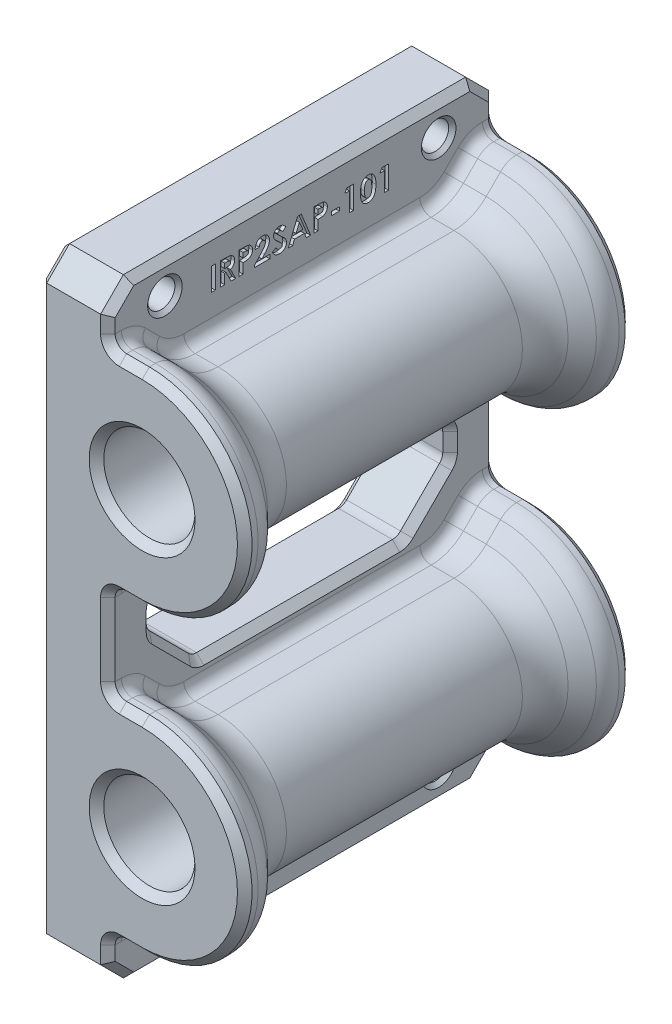
SolidWorks part; units mm, degrees
material "6061-T6 (SS)"
ref_plane "Front" through (0, 0, 0) normal (0, 0, 1) x (1, 0, 0)
ref_plane "Top" through (0, 0, 0) normal (0, 1, 0) x (1, 0, 0)
ref_plane "Right" through (0, 0, 0) normal (1, 0, 0) x (0, 0, -1)
sketch "Sketch1" plane through (0, 0, 0) normal (0, 0, 1) x (1, 0, 0)
  line L0 (0, 0) -> (0, -84.7725)
  line L1 (0, -84.7725) -> (14.2875, -84.7725)
  line L2 (14.2875, -84.7725) -> (14.2875, -77.6287)
  line L3 (14.2875, -49.0538) -> (14.2875, -35.7188)
  line L4 (14.2875, -7.1437) -> (14.2875, 0)
  line L5 (14.2875, 0) -> (0, 0)
  line L6 (7.9375, -21.4312) -> (0, -21.4312) construction
  arc A0 (14.2875, -77.6287) -> (14.2875, -49.0538) centre (14.2875, -63.3413) ccw
  arc A1 (14.2875, -35.7188) -> (14.2875, -7.1437) centre (14.2875, -21.4312) ccw
  circle A2 centre (14.2875, -21.4312) radius 6.35
  circle A3 centre (14.2875, -63.3413) radius 6.35
  arc A4 (14.2875, -7.1437) -> (14.2875, -35.7188) centre (14.2875, -21.4312) ccw construction
  point P7 (10.7057, -66.3674)
  point P15 (0, 0)
  dimension "D3" = 14.2875
  dimension "D6" = 12.7
  dimension "D1" = 84.7725
  dimension "D2" = 41.91
  dimension "D4" = 14.2875
extrude "Boss-Extrude1" add sketch "Sketch1" along normal blind 53.975
sketch "Sketch8" plane through (14.2875, 0, 0) normal (1, 0, 0) x (0, 0, -1)
  line L0 (-50.8, -35.7188) -> (-46.0375, -30.9563)
  line L1 (-53.975, -35.7188) -> (0, -35.7188) construction
  line L2 (-46.0375, -30.9563) -> (-7.9375, -30.9563)
  line L3 (-7.9375, -30.9563) -> (-3.175, -35.7188)
  line L4 (-3.175, -35.7188) -> (-50.8, -35.7188)
  line L5 (-53.975, -21.4313) -> (0, -21.4313) construction
  line L6 (-53.975, -7.1437) -> (-53.975, -35.7188) construction
  line L7 (0, -35.7188) -> (0, -7.1437) construction
  line L8 (-50.8, -35.7188) -> (-3.175, -35.7188)
  dimension "D1" = 3.175
  dimension "D2" = 45
  dimension "D3" = 19.05
  dimension "D4" = 3.175
revolve "Cut-Revolve1" cut sketch "Sketch8" angle 180 about L5
ref_plane "Plane1" through (0, -42.3862, 0) normal (0, -1, 0) x (-1, 0, 0)
mirror "Mirror1" about plane through (0, -42.3862, 0) normal (0, -1, 0) of "Cut-Revolve1"
sketch "Sketch9" plane through (14.2875, 0, 0) normal (1, 0, 0) x (0, 0, -1)
  line L0 (0, -7.1438) -> (0, 0) construction
  line L1 (0, 0) -> (-53.975, 0) construction
  line L2 (-53.975, 0) -> (-53.975, -7.1438) construction
  line L3 (-53.975, -7.1438) -> (-50.8, -7.1438) construction
  line L4 (-50.8, -7.1438) -> (-46.0375, -11.9062) construction
  line L5 (-46.0375, -11.9062) -> (-7.9375, -11.9063) construction
  line L6 (-7.9375, -11.9063) -> (-3.175, -7.1438) construction
  line L7 (-3.175, -7.1438) -> (0, -7.1438) construction
  line L8 (0, -49.0538) -> (0, -35.7188) construction
  line L9 (0, -35.7188) -> (-3.175, -35.7188) construction
  line L10 (-3.175, -35.7188) -> (-7.9375, -30.9563) construction
  line L11 (-7.9375, -30.9563) -> (-46.0375, -30.9563) construction
  line L12 (-46.0375, -30.9563) -> (-50.8, -35.7188) construction
  line L13 (-50.8, -35.7188) -> (-53.975, -35.7188) construction
  line L14 (-53.975, -35.7188) -> (-53.975, -49.0538) construction
  line L15 (-53.975, -49.0538) -> (-50.8, -49.0537) construction
  line L16 (-50.8, -49.0537) -> (-46.0375, -53.8162) construction
  line L17 (-46.0375, -53.8162) -> (-7.9375, -53.8162) construction
  line L18 (-7.9375, -53.8162) -> (-3.175, -49.0538) construction
  line L19 (-3.175, -49.0538) -> (0, -49.0538) construction
  line L20 (0, -84.7725) -> (0, -77.6287) construction
  line L21 (0, -77.6287) -> (-3.175, -77.6287) construction
  line L22 (-3.175, -77.6287) -> (-7.9375, -72.8662) construction
  line L23 (-7.9375, -72.8662) -> (-46.0375, -72.8662) construction
  line L24 (-46.0375, -72.8662) -> (-50.8, -77.6287) construction
  line L25 (-50.8, -77.6287) -> (-53.975, -77.6287) construction
  line L26 (-53.975, -77.6287) -> (-53.975, -84.7725) construction
  line L27 (-53.975, -84.7725) -> (0, -84.7725) construction
  line L28 (0, -7.1438) -> (0, 0)
  line L29 (0, 0) -> (-53.975, 0)
  line L30 (-53.975, 0) -> (-53.975, -7.1438)
  line L31 (-53.975, -7.1438) -> (-50.8, -7.1438)
  line L32 (-50.8, -7.1438) -> (-46.0375, -11.9062)
  line L33 (-46.0375, -11.9062) -> (-7.9375, -11.9063)
  line L34 (-7.9375, -11.9063) -> (-3.175, -7.1438)
  line L35 (-3.175, -7.1438) -> (0, -7.1438)
  line L36 (0, -49.0538) -> (0, -35.7188)
  line L37 (0, -35.7188) -> (-3.175, -35.7188)
  line L38 (-3.175, -35.7188) -> (-7.9375, -30.9563)
  line L39 (-7.9375, -30.9563) -> (-46.0375, -30.9563)
  line L40 (-46.0375, -30.9563) -> (-50.8, -35.7188)
  line L41 (-50.8, -35.7188) -> (-53.975, -35.7188)
  line L42 (-53.975, -35.7188) -> (-53.975, -49.0538)
  line L43 (-53.975, -49.0538) -> (-50.8, -49.0537)
  line L44 (-50.8, -49.0537) -> (-46.0375, -53.8162)
  line L45 (-46.0375, -53.8162) -> (-7.9375, -53.8162)
  line L46 (-7.9375, -53.8162) -> (-3.175, -49.0538)
  line L47 (-3.175, -49.0538) -> (0, -49.0538)
  line L48 (0, -84.7725) -> (0, -77.6287)
  line L49 (0, -77.6287) -> (-3.175, -77.6287)
  line L50 (-3.175, -77.6287) -> (-7.9375, -72.8662)
  line L51 (-7.9375, -72.8662) -> (-46.0375, -72.8662)
  line L52 (-46.0375, -72.8662) -> (-50.8, -77.6287)
  line L53 (-50.8, -77.6287) -> (-53.975, -77.6287)
  line L54 (-53.975, -77.6287) -> (-53.975, -84.7725)
  line L55 (-53.975, -84.7725) -> (0, -84.7725)
extrude "Cut-Extrude3" cut sketch "Sketch9" against normal offset from surface (4.7625 mm away) 9.525 up to face at (0, -42.3862, 26.9875)
fillet "Fillet2" radius 6.35 12 edges at (11.9062, -11.9063, 7.9375) (11.9062, -30.9563, 7.9375) (11.9062, -11.9062, 46.0375) (11.9062, -30.9563, 46.0375) (11.9062, -72.8662, 7.9375) (11.9062, -53.8162, 7.9375) (11.9062, -72.8662, 46.0375) (11.9062, -53.8162, 46.0375) (23.8125, -21.4313, 7.9375) (23.8125, -21.4313, 46.0375) (23.8125, -63.3412, 7.9375) (23.8125, -63.3413, 46.0375)
fillet "Fillet3" radius 3.175 12 edges at (11.9062, -7.1438, 3.175) (11.9062, -35.7188, 3.175) (11.9062, -7.1438, 50.8) (11.9062, -35.7188, 50.8) (11.9062, -77.6287, 3.175) (11.9062, -49.0538, 3.175) (11.9062, -77.6287, 50.8) (11.9062, -49.0537, 50.8) (28.575, -21.4313, 3.175) (28.575, -21.4312, 50.8) (28.575, -63.3412, 3.175) (28.575, -63.3412, 50.8)
hole_wizard "#6 Clearance Hole1" positions "Sketch2" profile "Sketch3" hole size "#6" standard "ANSI Inch" end condition through all
sketch "Sketch2" plane through (9.525, 0, 0) normal (1, 0, 0) x (0, 0, -1)
  line L0 (-46.0375, -4.445) -> (-7.9375, -4.445) construction
  line L1 (-7.9375, -4.445) -> (-7.9375, -80.3275) construction
  line L2 (-7.9375, -80.3275) -> (-46.0375, -80.3275) construction
  line L3 (-46.0375, -80.3275) -> (-46.0375, -4.445) construction
  line L8 (-53.975, 0) -> (-46.0375, -4.445) construction
  line L9 (-46.0375, -4.445) -> (-53.975, -7.1438) construction
  line L11 (-7.9375, -4.445) -> (0, 0) construction
  line L13 (-7.9375, -4.445) -> (0, -7.1438) construction
  line L15 (0, -84.7725) -> (-7.9375, -80.3275) construction
  line L16 (-7.9375, -80.3275) -> (0, -77.6287) construction
  line L19 (-53.975, -7.1438) -> (-53.975, 0) construction
  line L22 (-53.975, 0) -> (0, 0) construction
  point P0 (-46.0375, -4.445)
  point P2 (-7.9375, -4.445)
  point P4 (-46.0375, -80.3275)
  point P6 (-7.9375, -80.3275)
  point P54 (0, 0)
  point P56 (0.7666, -3.5719)
  point P59 (0, -6.3154)
  point P61 (-52.0108, -4.9842)
  point P63 (0, 0)
  point P67 (-7.8344, -3.7926)
  point P68 (1.3227, -81.9017)
  point P73 (-8.6515, -4.9145)
  dimension "D1" = 7.9375
  dimension "D2" = 4.445
sketch "Sketch3" plane through (9.525, -4.445, 46.0375) normal (0, 1, 0) x (0, 0, -1)
  line L0 (0, 0) -> (0, 9.525)
  line L1 (0, 9.525) -> (1.8986, 9.525)
  line L2 (1.8986, 9.525) -> (1.8986, 0)
  line L5 (1.8986, 0) -> (0, 0)
  line L11 (0, -6.35) -> (0, 107.95) construction
  dimension "Thru Hole Dia." = 3.7973
  dimension "Thru Hole Depth" = 9.525
sketch "Sketch6" plane through (9.525, 0, 0) normal (1, 0, 0) x (0, 0, -1)
  line L0 (-41.275, -34.1313) -> (-47.625, -40.4813)
  line L1 (-47.625, -40.4813) -> (-47.625, -44.2913)
  line L2 (-47.625, -44.2913) -> (-41.275, -50.6412)
  line L3 (-41.275, -50.6412) -> (-12.7, -50.6412)
  line L4 (-12.7, -50.6412) -> (-6.35, -44.2913)
  line L5 (-6.35, -44.2913) -> (-6.35, -40.4813)
  line L6 (-6.35, -40.4813) -> (-12.7, -34.1312)
  line L7 (-12.7, -34.1312) -> (-41.275, -34.1313)
  line L8 (-26.9875, -34.1313) -> (-26.9875, -50.6412) construction
  line L13 (-10.5678, -53.8162) -> (-43.4072, -53.8162) construction
  line L14 (-43.4072, -30.9563) -> (-10.5678, -30.9563) construction
  line L15 (0, -35.7188) -> (0, -49.0538) construction
  line L16 (-53.975, -49.0538) -> (-53.975, -35.7188) construction
  point P10 (-5.6959, -38.1086)
  dimension "D1" = 3.175
  dimension "D2" = 3.175
  dimension "D3" = 6.35
  dimension "D4" = 6.35
  dimension "D5" = 6.35
extrude "Cut-Extrude1" cut sketch "Sketch6" against normal through all
fillet "Fillet1" radius 1.5875 44 edges at (4.7625, -50.6412, 12.7) (4.7625, -50.6412, 41.275) (4.7625, -44.2913, 47.625) (4.7625, -40.4813, 47.625) (4.7625, -34.1313, 41.275) (4.7625, -44.2913, 6.35) (4.7625, -40.4813, 6.35) (4.7625, -34.1312, 12.7) (9.525, -35.7188, 53.0451) (9.525, -35.4771, 50.9001) (9.525, -33.8025, 48.8837) (9.525, -31.4396, 45.8373) (9.525, -35.7188, 0.9299) (9.525, -35.4771, 3.0749) (9.525, -33.8025, 5.0913) (9.525, -31.4396, 8.1377) (9.525, -7.1438, 0.9299) (9.525, -7.3854, 3.0749) (9.525, -9.06, 5.0913) (9.525, -11.4229, 8.1377) (9.525, -7.1438, 53.0451) (9.525, -7.3854, 50.9001) (9.525, -9.06, 48.8837) (9.525, -11.4229, 45.8373) (9.525, -49.0538, 0.9299) (9.525, -49.2954, 3.0749) (9.525, -50.97, 5.0913) (9.525, -53.3329, 8.1377) (9.525, -49.0538, 53.0451) (9.525, -49.2954, 50.9001) (9.525, -50.97, 48.8837) (9.525, -53.3329, 45.8373) (9.525, -77.6287, 53.0451) (9.525, -77.3871, 50.9001) (9.525, -75.7125, 48.8837) (9.525, -73.3496, 45.8373) (9.525, -77.6287, 0.9299) (9.525, -77.3871, 3.0749) (9.525, -75.7125, 5.0913) (9.525, -73.3496, 8.1377) (9.525, -30.9563, 26.9875) (9.525, -11.9063, 26.9875) (9.525, -53.8162, 26.9875) (9.525, -72.8662, 26.9875)
chamfer "Chamfer2" distance 3.175 angle 45 4 edges at (4.7625, -84.7725, 0) (4.7625, -84.7725, 53.975) (4.7625, 0, 0) (4.7625, 0, 53.975)
chamfer "Chamfer1" distance 1.016 angle 45 76 edges at (20.6375, -63.3413, 0) (20.6375, -63.3413, 53.975) (20.6375, -21.4312, 0) (20.6375, -21.4312, 53.975) (0, -84.7725, 26.9875) (0, -83.185, 1.5875) (0, -42.3862, 0) (0, -1.5875, 1.5875) (0, 0, 26.9875) (0, -1.5875, 52.3875) (0, -42.3862, 53.975) (0, -83.185, 52.3875) (28.575, -63.3413, 0) (28.575, -63.3413, 53.975) (28.575, -21.4312, 0) (28.575, -21.4312, 53.975) (0, -47.4663, 44.45) (0, -50.5204, 41.2249) (0, -44.2412, 47.5042) (0, -50.6412, 26.9875) (0, -42.3863, 47.625) (0, -50.5204, 12.7501) (0, -40.5313, 47.5042) (0, -47.4663, 9.525) (0, -37.3063, 44.45) (0, -44.2412, 6.4708) (0, -34.2521, 41.2249) (0, -42.3863, 6.35) (0, -34.1313, 26.9875) (0, -40.5313, 6.4708) (0, -34.2521, 12.7501) (0, -37.3062, 9.525) (9.525, -83.185, 52.3875) (9.525, -84.7725, 26.9875) (9.525, -83.185, 1.5875) (9.525, -80.4069, 0) (9.525, -80.4069, 53.975) (9.99, -78.0937, 0) (9.99, -78.0937, 53.975) (12.7, -77.6287, 0) (12.7, -77.6287, 53.975) (12.7, -49.0538, 0) (12.7, -49.0538, 53.975) (9.99, -48.5888, 0) (9.99, -48.5888, 53.975) (9.525, -42.3863, 0) (9.525, -42.3863, 53.975) (9.99, -36.1837, 0) (9.99, -36.1837, 53.975) (12.7, -35.7188, 0) (12.7, -35.7188, 53.975) (12.7, -7.1438, 0) (12.7, -7.1438, 53.975) (9.99, -6.6788, 0) (9.99, -6.6788, 53.975) (9.525, -4.3656, 0) (9.525, -1.5875, 1.5875) (9.525, 0, 26.9875) (9.525, -1.5875, 52.3875) (9.525, -4.3656, 53.975) (9.525, -50.6412, 26.9875) (9.525, -50.5204, 12.7501) (9.525, -50.5204, 41.2249) (9.525, -47.4663, 9.525) (9.525, -47.4663, 44.45) (9.525, -44.2412, 6.4708) (9.525, -44.2412, 47.5042) (9.525, -42.3863, 6.35) (9.525, -42.3863, 47.625) (9.525, -40.5313, 6.4708) (9.525, -40.5313, 47.5042) (9.525, -37.3062, 9.525) (9.525, -37.3063, 44.45) (9.525, -34.2521, 12.7501) (9.525, -34.2521, 41.2249) (9.525, -34.1313, 26.9875)
chamfer "Chamfer3" distance 0.508 angle 45 8 edges at (0, -80.3275, 6.0388) (0, -80.3275, 44.1388) (0, -4.445, 6.0389) (0, -4.445, 44.1388) (9.525, -80.3275, 6.0388) (9.525, -80.3275, 44.1388) (9.525, -4.445, 6.0389) (9.525, -4.445, 44.1388)
sketch "Sketch7" plane through (9.525, 0, 0) normal (1, 0, 0) x (0, 0, -1)
  line L0 (-26.9875, -1.016) -> (-26.9875, -7.2549) construction
  line L2 (-26.9875, -7.2549) -> (-26.9875, -4.0799) construction
  line L3 (-26.9875, -4.0799) -> (-26.9875, -10.3188) construction
  line L4 (-52.959, -3.5958) -> (-52.959, -5.5563) construction
  line L5 (-52.959, -7.2549) -> (-1.016, -7.2549) construction
  line L9 (-1.016, -5.5563) -> (-1.016, -3.5958) construction
  line L10 (-43.4072, -10.3188) -> (-10.5678, -10.3188) construction
  line L11 (-3.5958, -1.016) -> (-50.3792, -1.016) construction
  text T0 "<b>IRP2SAP-101</b>" font "Century Gothic" height 3.175
  point P2 (0, 0)
  point P8 (0, 0)
  point P12 (0, 0)
  point P15 (0, 0)
  point P19 (-31.3376, -1.016)
  point P20 (-1.016, -6.291)
  point P21 (0, 0)
  dimension "D1" = 3.175
extrude "Cut-Extrude2" cut sketch "Sketch7" against normal blind 0.508
